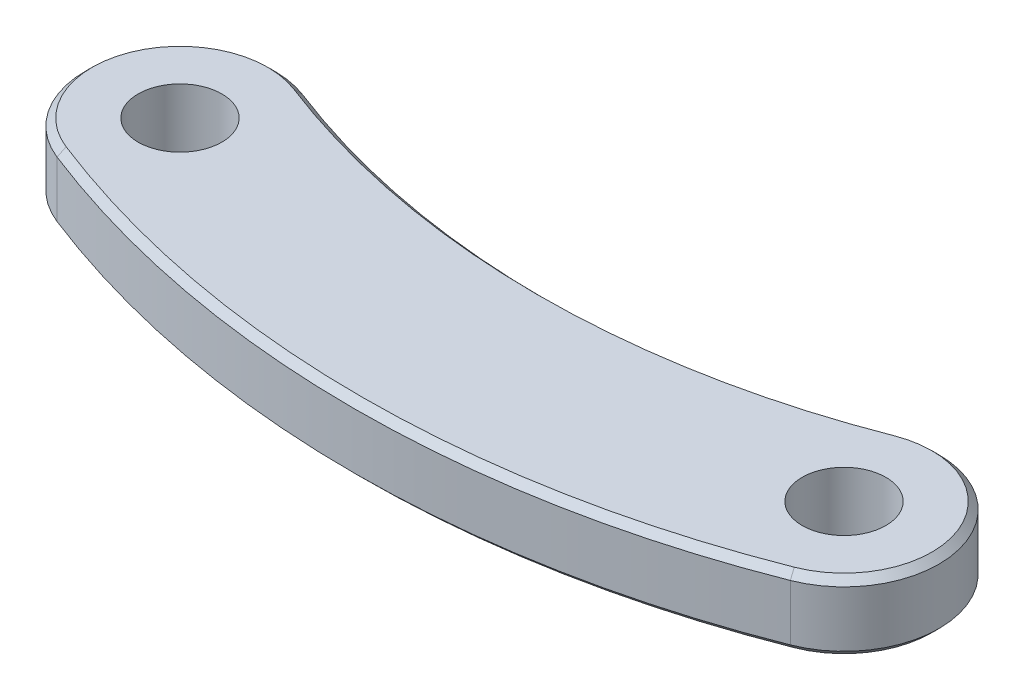
SolidWorks part; units mm, degrees
ref_plane "前视基准面" through (0, 0, 0) normal (0, 0, 1) x (1, 0, 0)
ref_plane "上视基准面" through (0, 0, 0) normal (0, 1, 0) x (1, 0, 0)
ref_plane "右视基准面" through (0, 0, 0) normal (1, 0, 0) x (0, 0, -1)
sketch "草图1" plane through (0, 0, 0) normal (0, 1, 0) x (1, 0, 0)
  line L0 (0, 0) -> (47.6, 0) construction
  circle A0 centre (0, 0) radius 3
  circle A1 centre (47.6, 0) radius 3
  arc A2 (45.1404, 6.3396) -> (50.0822, -6.3308) centre (47.6, 0) cw
  arc A3 (2.4596, 6.3396) -> (-2.4822, -6.3308) centre (0, 0) ccw
  arc A4 (-2.4822, -6.3308) -> (50.0822, -6.3308) centre (23.8, 60.7009) ccw
  arc A5 (2.4596, 6.3396) -> (45.1404, 6.3396) centre (23.8, 61.3449) ccw
  dimension "D2" = 6
  dimension "D3" = 6.8
  dimension "D4" = 72
  dimension "D5" = 59
  dimension "D1" = 47.6
extrude "凸台-拉伸1" add sketch "草图1" along normal blind 5
chamfer "倒角1" distance 0.5 angle 45 8 edges at (23.8, 0, -2.3449) (-6.3352, 0, -2.4709) (53.9352, 0, -2.4709) (23.8, 0, 11.2991) (23.8, 5, -2.3449) (-6.3352, 5, -2.4709) (53.9352, 5, -2.4709) (23.8, 5, 11.2991)
